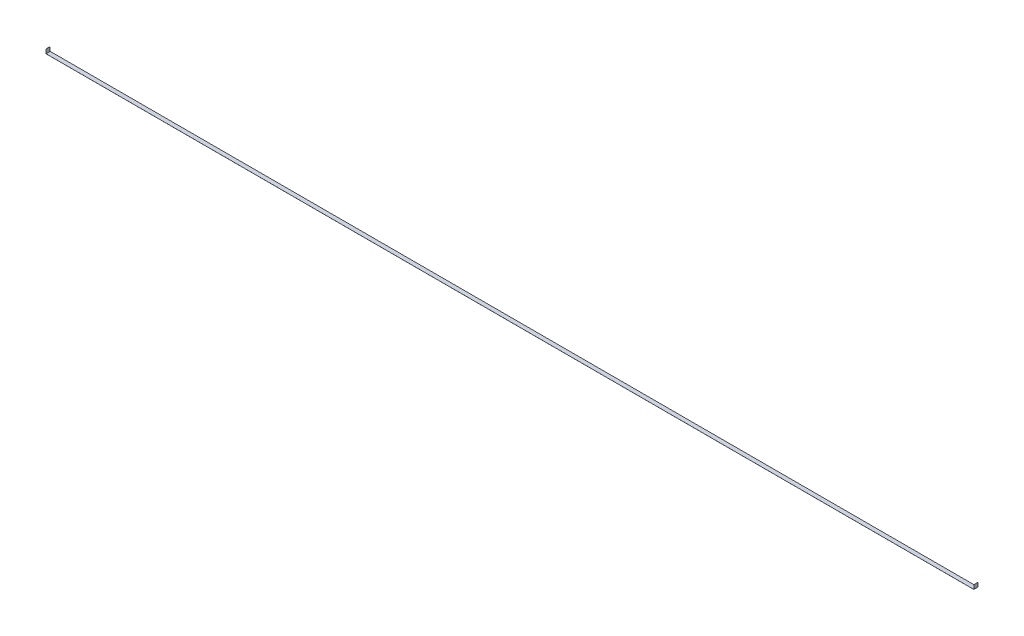
SolidWorks part; units mm, degrees
material "Nylon 101"
ref_plane "Front Plane" through (0, 0, 0) normal (0, 0, 1) x (1, 0, 0)
ref_plane "Top Plane" through (0, 0, 0) normal (0, 1, 0) x (1, 0, 0)
ref_plane "Right Plane" through (0, 0, 0) normal (1, 0, 0) x (0, 0, -1)
sketch "Sketch1" plane through (0, 0, 0) normal (0, 0, 1) x (1, 0, 0)
  line L0 (-2832.1, 0) -> (2832.1, 0)
  line L1 (2832.1, 0) -> (2832.1, 25.4)
  line L3 (-2832.1, 25.4) -> (-2832.1, 0)
  point P4 (0, 0)
  dimension "D1" = 25.4
  dimension "D2" = 5664.2
extrude "Extrude-Thin1" add sketch "Sketch1" along normal mid plane 25.4 thin
